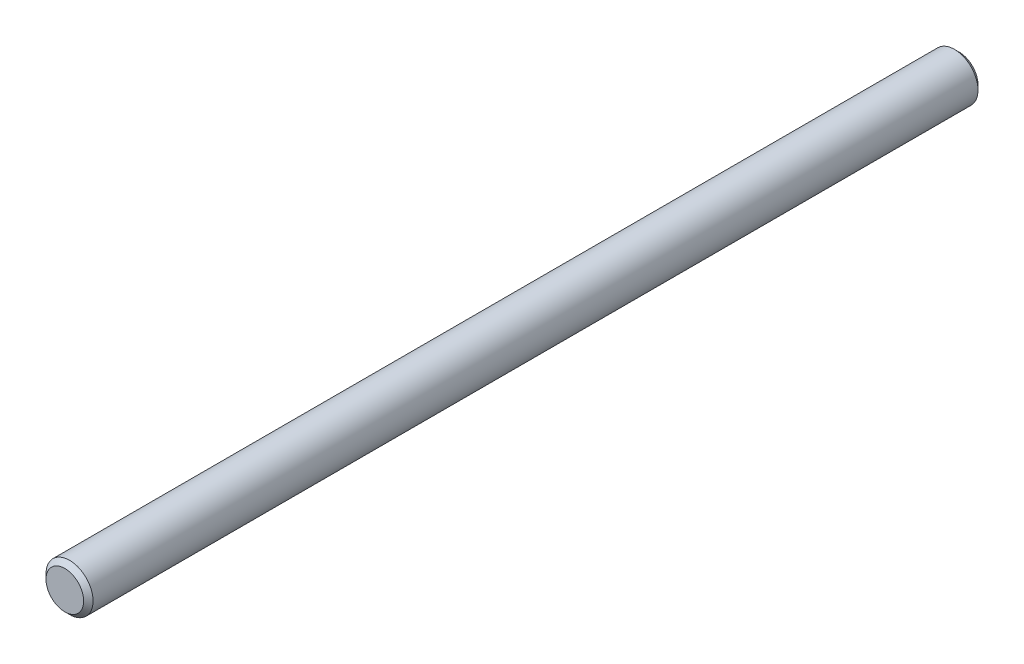
SolidWorks part; units mm, degrees
ref_plane "Plan de face" through (0, 0, 0) normal (0, 0, 1) x (1, 0, 0)
ref_plane "Plan de dessus" through (0, 0, 0) normal (0, 1, 0) x (1, 0, 0)
ref_plane "Plan de droite" through (0, 0, 0) normal (1, 0, 0) x (0, 0, -1)
sketch "Sketch1" plane through (0, 0, 0) normal (0, 0, 1) x (1, 0, 0)
  circle A0 centre (0, 0) radius 3.175
  dimension "D1" = 6.35
extrude "Boss-Extrude1" add sketch "Sketch1" along normal mid plane 120.65
chamfer "Chamfer1" distance 0.635 angle 45 2 edges at (3.175, 0, -60.325) (3.175, 0, 60.325)
equation "\"Cout/Uni\"= ( ( \"Coût Achat\" + \"Coût Modif\" ) / \"Nb/Paquet\" )"
